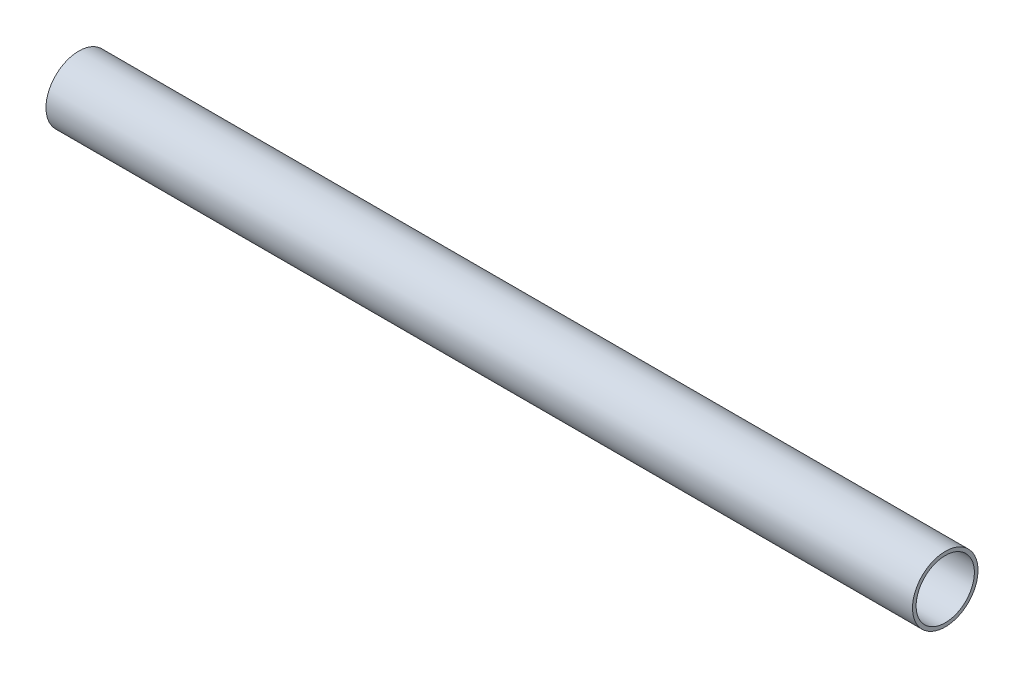
SolidWorks part; units mm, degrees
material "AISI 1020"
ref_plane "Спереди" through (0, 0, 0) normal (0, 0, 1) x (1, 0, 0)
ref_plane "Сверху" through (0, 0, 0) normal (0, 1, 0) x (1, 0, 0)
ref_plane "Справа" through (0, 0, 0) normal (1, 0, 0) x (0, 0, -1)
sketch "Эскиз1" plane through (0, 0, 0) normal (1, 0, 0) x (0, 0, -1)
  circle B0 centre (0, 0) radius 12
  circle B1 centre (0, 0) radius 13.5
sketch_block_instance "DN25-27x1.5-1"
sketch_block "DN25-27x1.5" parameters "D2"=27, "D1"=1.5
extrude "Бобышка-Вытянуть1" add sketch "Эскиз1" along normal offset from surface (357 mm away) 5
